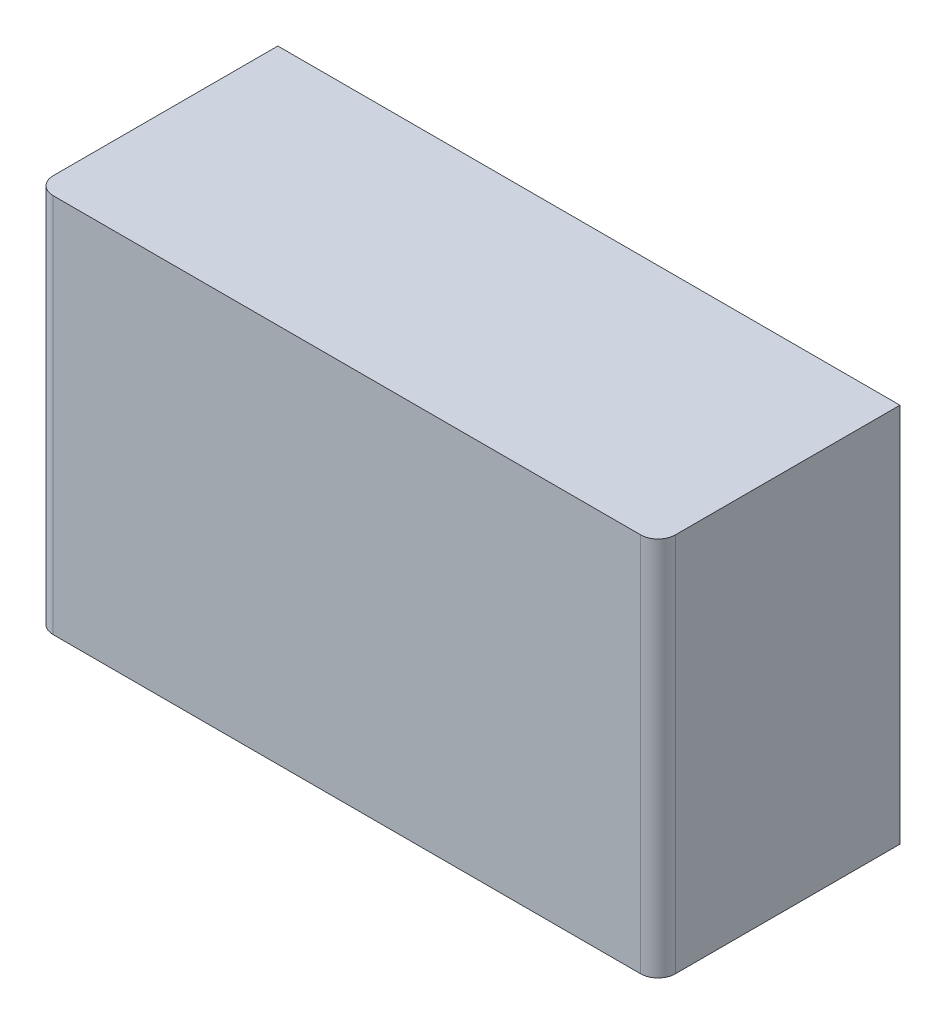
SolidWorks part; units mm, degrees
ref_plane "Front Plane" through (0, 0, 0) normal (0, 0, 1) x (1, 0, 0)
ref_plane "Top Plane" through (0, 0, 0) normal (0, 1, 0) x (1, 0, 0)
ref_plane "Right Plane" through (0, 0, 0) normal (1, 0, 0) x (0, 0, -1)
sketch "Sketch1" plane through (0, 0, 0) normal (0, 1, 0) x (1, 0, 0)
  line L1 (-457.2, -177.8) -> (457.2, -177.8)
  line L2 (-457.2, -177.8) -> (-457.2, 177.8)
  line L3 (-457.2, 177.8) -> (457.2, 177.8)
  line L4 (457.2, -177.8) -> (457.2, 177.8)
  line L5 (-457.2, -177.8) -> (457.2, 177.8) construction
  line L6 (-457.2, 177.8) -> (457.2, -177.8) construction
  point P0 (0, 0)
  dimension "D1" = 355.6
  dimension "D2" = 914.4
extrude "Boss-Extrude1" add sketch "Sketch1" along normal blind 558.8
fillet "Fillet1" radius 25.4 2 edges at (457.2, 279.4, 177.8) (-457.2, 279.4, 177.8)
